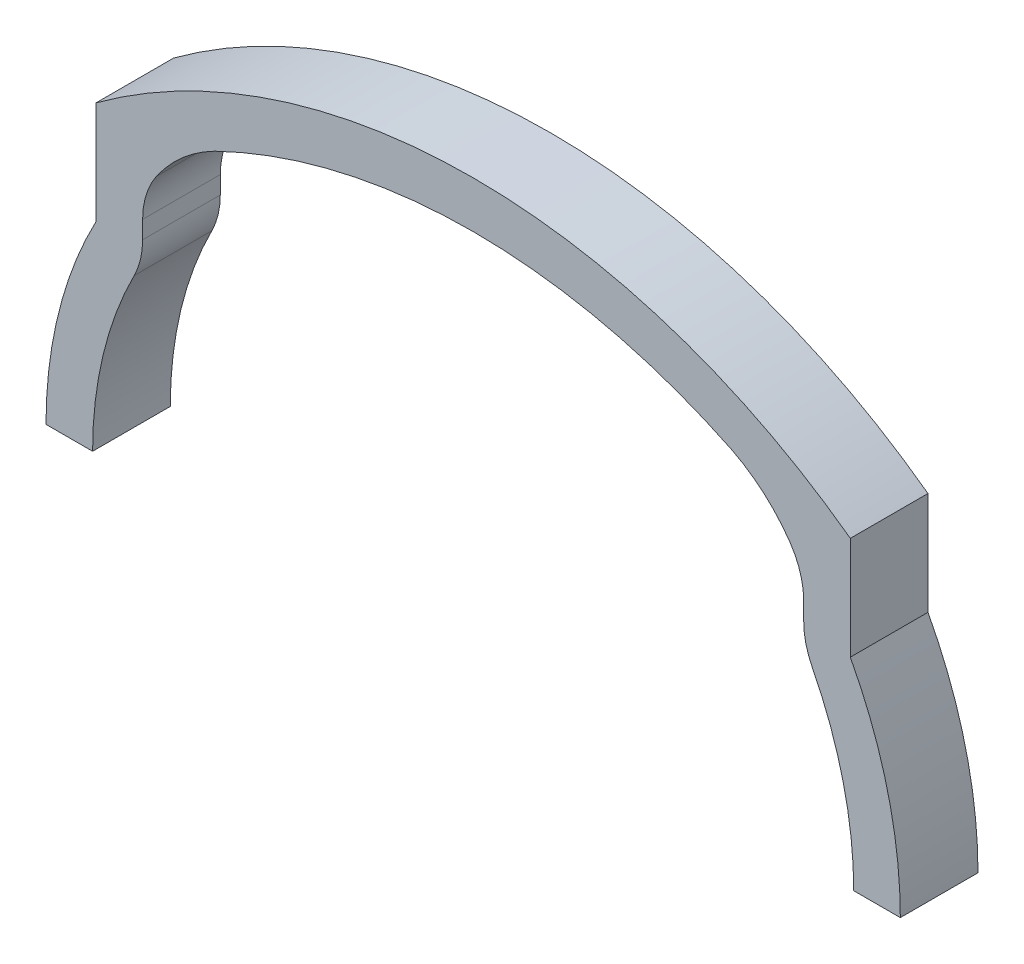
SolidWorks part; units mm, degrees
ref_plane "Front Plane" through (0, 0, 0) normal (0, 0, 1) x (1, 0, 0)
ref_plane "Top Plane" through (0, 0, 0) normal (0, 1, 0) x (1, 0, 0)
ref_plane "Right Plane" through (0, 0, 0) normal (1, 0, 0) x (0, 0, -1)
sketch "Sketch1" plane through (0, 0, 0) normal (0, 0, 1) x (1, 0, 0)
  line L1 (67.3394, 0) -> (0, 0) construction
  line L2 (0, 0) -> (0, 65.2519) construction
  line L4 (-21, 17.5685) -> (-19.0192, 14.638) construction
  line L5 (21, 17.5685) -> (19.0192, 14.638) construction
  line L6 (-24.5, 0) -> (24.5, 0)
  line L8 (-21.28, 14.5401) -> (-21.28, 13.4019)
  line L9 (21.28, 14.5401) -> (21.28, 13.4019)
  line L12 (24.28, 19.5376) -> (24.28, 12.9125)
  line L13 (-24.28, 19.5376) -> (-24.28, 12.9125)
  line L14 (-27.5, 0) -> (27.5, 0)
  line L15 (-21.28, 17.9827) -> (-21.28, 12.1413) construction
  line L16 (21.28, 17.9827) -> (21.28, 12.1413) construction
  line L17 (-27.3359, -3) -> (27.3359, -3) construction
  arc A2 (21, 17.5685) -> (-21, 17.5685) centre (0, -13.5) ccw construction
  arc A4 (24.5, 0) -> (21.8258, 11.1304) centre (0, 0) ccw
  arc A6 (16.6444, 20.6609) -> (-16.6444, 20.6609) centre (0, -13.5) ccw
  arc A8 (-21.8258, 11.1304) -> (-24.5, 0) centre (0, 0) ccw
  arc A9 (24.5, 0) -> (-24.5, 0) centre (0, 0) ccw construction
  arc A10 (24, 0) -> (-24, 0) centre (0, 0) ccw construction
  arc A11 (27.5, 0) -> (24.28, 12.9125) centre (0, 0) ccw
  arc A12 (24.28, 19.5376) -> (-24.28, 19.5376) centre (0, -13.5) ccw
  arc A13 (-24.28, 12.9125) -> (-27.5, 0) centre (0, 0) ccw
  arc A14 (-24.28, 12.9125) -> (-27.3359, -3) centre (0, 0) ccw construction
  arc A15 (27.3359, -3) -> (24.28, 12.9125) centre (0, 0) ccw construction
  arc A18 (21.28, 17.9827) -> (-21.28, 17.9827) centre (0, -13.5) ccw construction
  arc A19 (-16.6444, 20.6609) -> (-20.3928, 17.3836) centre (-12.0318, 11.6031) ccw
  arc A20 (16.6444, 20.6609) -> (20.3928, 17.3836) centre (12.0318, 11.6031) cw
  arc A21 (24.5, 0) -> (21.28, 12.1413) centre (0, 0) ccw construction
  arc A22 (21.28, 13.4019) -> (21.8258, 11.1304) centre (26.28, 13.4019) ccw
  arc A23 (20.3928, 17.3836) -> (21.28, 14.5401) centre (16.28, 14.5401) cw
  arc A24 (-21.28, 12.1413) -> (-24.5, 0) centre (0, 0) ccw construction
  arc A25 (-21.28, 13.4019) -> (-21.8258, 11.1304) centre (-26.28, 13.4019) cw
  arc A26 (-20.3928, 17.3836) -> (-21.28, 14.5401) centre (-16.28, 14.5401) ccw
  point P4 (0, 24)
  point P5 (0, 24)
  point P32 (-21.28, 15.821)
  point P44 (21.28, 15.821)
  point P50 (-21.28, 15.821)
  dimension "D1" = 24
  dimension "D2" = 75
  dimension "D6" = 5
  dimension "D3" = 42
  dimension "D4" = 0.5
  dimension "D5" = 3
extrude "Boss-Extrude3" add sketch "Sketch1" along normal blind 5 contours A6 A20 L9 A4 L14 A11 L12 A12 L13 A13 A8 L8 A19
